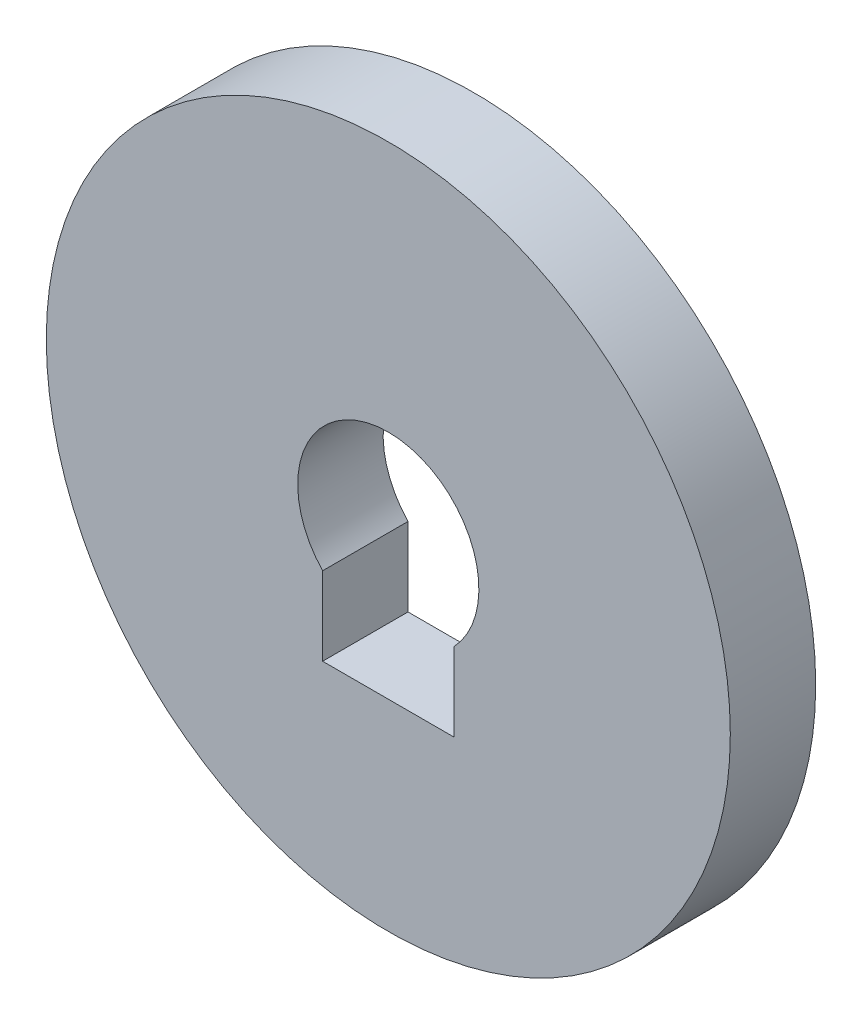
SolidWorks part; units mm, degrees
ref_plane "Front Plane" through (0, 0, 0) normal (0, 0, 1) x (1, 0, 0)
ref_plane "Top Plane" through (0, 0, 0) normal (0, 1, 0) x (1, 0, 0)
ref_plane "Right Plane" through (0, 0, 0) normal (1, 0, 0) x (0, 0, -1)
sketch "Sketch1" plane through (0, 0, 0) normal (0, 0, 1) x (1, 0, 0)
  line L0 (0, -228) -> (0, 0)
  line L5 (0, 0) -> (0, 65)
  line L7 (0, -228) -> (0, -364.5)
  line L12 (70, -150) -> (-70, -150)
  line L13 (-70, -66.4671) -> (-70, -150)
  line L14 (70, -66.4671) -> (70, -150)
  circle A6 centre (0, 0) radius 364.5
  circle A18 centre (0, 0) radius 96.5291
  point P0 (0, 0)
  dimension "D1" = 0
  dimension "D2" = 65
  dimension "D3" = 228
  dimension "D6" = 136.5
extrude "Boss-Extrude2" add sketch "Sketch1" along normal blind 91
